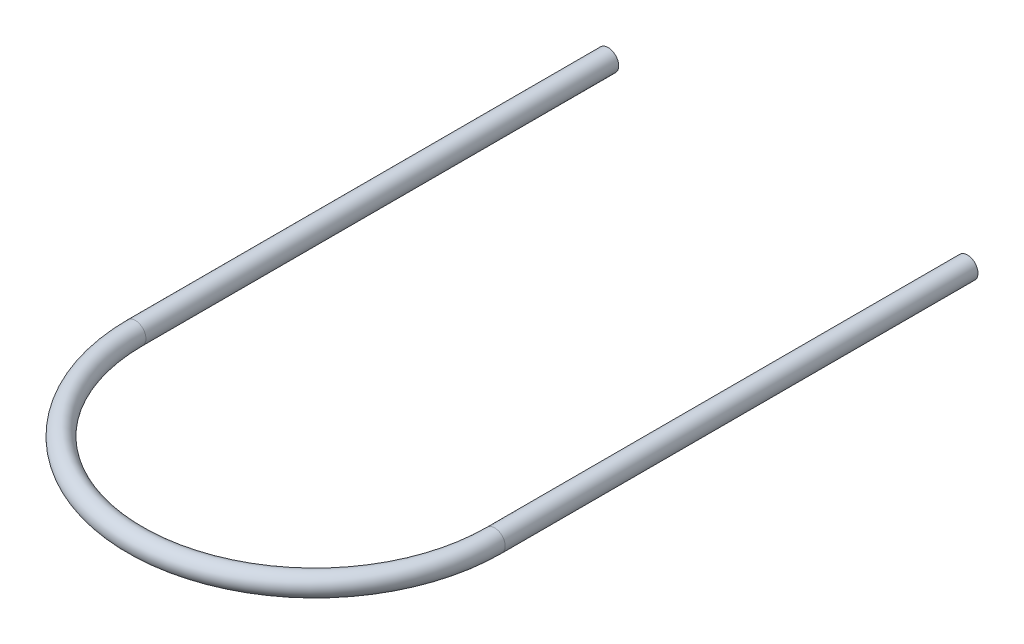
SolidWorks part; units mm, degrees
ref_plane "Front Plane" through (0, 0, 0) normal (0, 0, 1) x (1, 0, 0)
ref_plane "Top Plane" through (0, 0, 0) normal (0, 1, 0) x (1, 0, 0)
ref_plane "Right Plane" through (0, 0, 0) normal (1, 0, 0) x (0, 0, -1)
sketch "Sketch2" plane through (0, 0, 0) normal (0, 1, 0) x (1, 0, 0)
  line L0 (-241.3, 0) -> (-241.3, 635)
  line L1 (241.3, 0) -> (241.3, 635)
  arc A0 (-241.3, 0) -> (241.3, 0) centre (0, 0) ccw
  point P1 (0, 0)
  point P9 (0, -241.3)
  dimension "D1" = 241.3
  dimension "D2" = 635
  dimension "D3" = 635
sweep "Sweep3" add path "Sketch2" circular profile diameter 28.448 parameters "D3"=28.448
